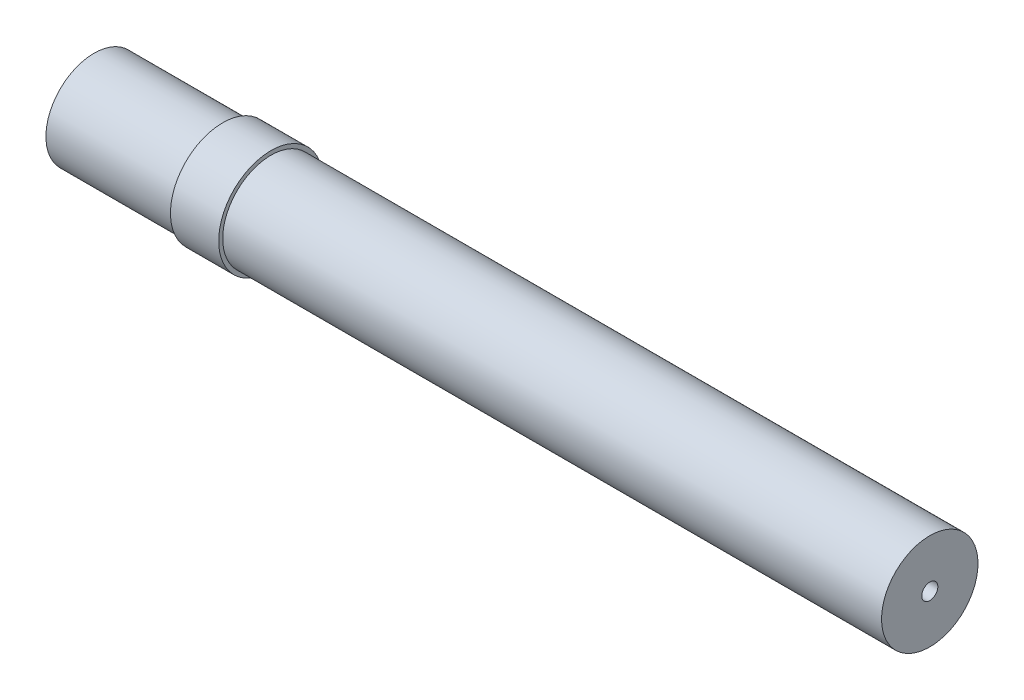
SolidWorks part; units mm, degrees
material "Tantalum"
ref_plane "Front Plane" through (0, 0, 0) normal (0, 0, 1) x (1, 0, 0)
ref_plane "Top Plane" through (0, 0, 0) normal (0, 1, 0) x (1, 0, 0)
ref_plane "Right Plane" through (0, 0, 0) normal (1, 0, 0) x (0, 0, -1)
sketch "Sketch1" plane through (0, 0, 0) normal (0, 0, 1) x (1, 0, 0)
  line L2 (11, 3.25) -> (-41, 3.25) construction
  line L3 (10, 0.5) -> (11, 0.5)
  line L4 (10, 0.5) -> (10, 2.25)
  line L5 (10, 2.25) -> (-41, 2.25)
  line L9 (-41, 2.25) -> (-41, 3.25) construction
  line L18 (-30, 3.25) -> (-30, 3)
  line L19 (-30, 3) -> (11, 3)
  line L20 (11, 3) -> (11, 0.5)
  line L21 (-30, 3) -> (-41, 3) construction
  line L22 (-33, 3.25) -> (-33, 3)
  line L23 (-41, 3) -> (-41, 2.25)
  line L24 (-30, 3.25) -> (-33, 3.25)
  line L25 (-33, 3) -> (-41, 3)
  dimension "D1" = 3.25
  dimension "D2" = 2.75
  dimension "D3" = 1
  dimension "D4" = 1
  dimension "D5" = 0.25
  dimension "D6" = 10
  dimension "D7" = 8
  dimension "D8" = 3
ref_axis "Axis1" through (13.5, 0, 0) along (-1, 0, 0)
revolve "Revolve1" add sketch "Sketch1" angle 360 about axis through (13.5, 0, 0) along (-1, 0, 0)
other "#12-28 Machine Threads Stud1" [suppressed] parameters "D1"=5.4864, "D2"=10, "D3"=8, "D4"=6
sketch "Sketch15" plane through (-42.5, 0, 0) normal (0, 1, 0) x (0, 0, -1)
  line L5 (0, -14.3089) -> (0, 0) construction
  line L6 (2.2022, 0) -> (2.7432, -0.541)
  line L9 (2.7432, -0.541) -> (2.7432, -8)
  line L10 (2.2022, 0) -> (3, 0)
  line L11 (3, 0) -> (3, -8)
  line L12 (2.7432, -8) -> (3, -8)
  dimension "Minor Diameter" = 4.4044
  dimension "Major Diameter" = 5.4864
  dimension "Thread Length" = 8
  dimension "Cylinder Diameter" = 6
  dimension "Chamfer Angle" = 45
cosmetic thread "Stud Thread1" [suppressed] parameters "D1"=8, "D2"=4.4044
thread "Thread5" [suppressed] pitch 0.8 start angle 0, offset 0, length 8, pitch 0.8, diameter 5.4864
ref_plane "Plane6" through (-41.959, 0, -2.7432) normal (0, -1, 0) x (0, 0, -1)
sketch "Thread Profile6" plane through (-41.959, 0, -2.7432) normal (0, -1, 0) x (0, 0, -1)
  line L0 (0, 0) -> (0, 0.8) construction
  line L1 (0, 0) -> (0.433, 0.25)
  line L2 (0.433, 0.25) -> (0.433, 0.35)
  line L3 (0.433, 0.35) -> (0, 0.6)
  line L4 (0.433, 0.3) -> (0, 0.3) construction
  line L11 (0, 0) -> (0, 0.6)
  point P2 (0, 0)
  dimension "Pitch" = 0.8
  dimension "Profile_Angle" = 60
  dimension "Profile_Land" = 0.1
  dimension "Profile_Height" = 0.433
